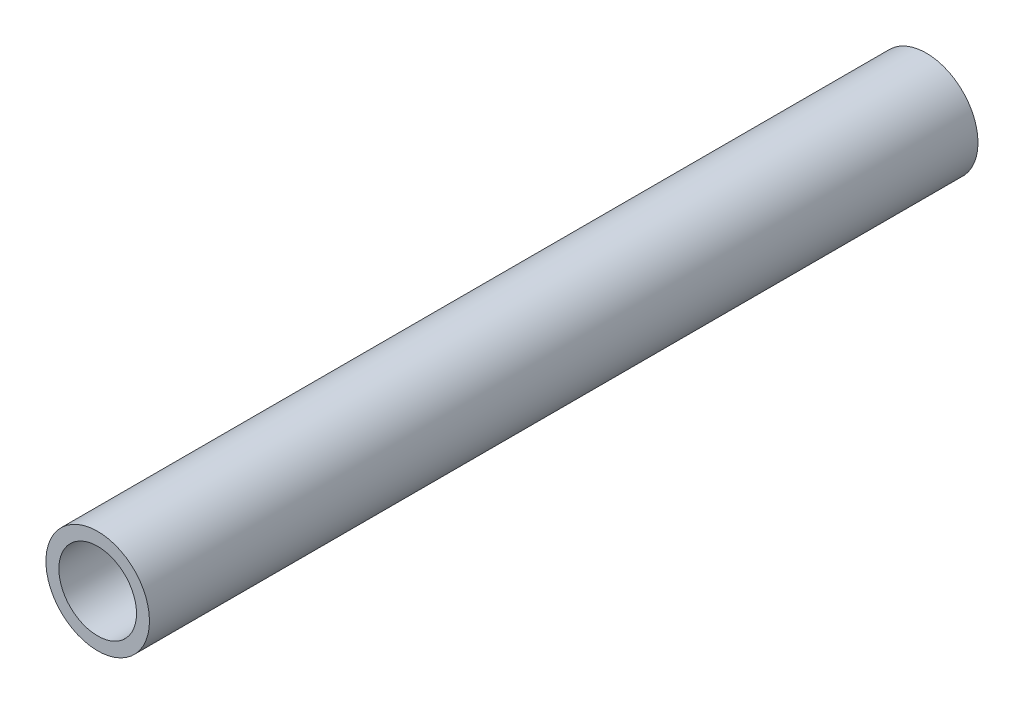
SolidWorks part; units mm, degrees
ref_plane "Front Plane" through (0, 0, 0) normal (0, 0, 1) x (1, 0, 0)
ref_plane "Top Plane" through (0, 0, 0) normal (0, 1, 0) x (1, 0, 0)
ref_plane "Right Plane" through (0, 0, 0) normal (1, 0, 0) x (0, 0, -1)
sketch "Sketch1" plane through (0, 0, 0) normal (0, 0, 1) x (1, 0, 0)
  circle A0 centre (0, 0) radius 3.175
  circle A1 centre (0, 0) radius 2.3813
  dimension "D1" = 6.35
  dimension "D2" = 4.7625
extrude "Boss-Extrude1" add sketch "Sketch1" along normal blind 50.8
